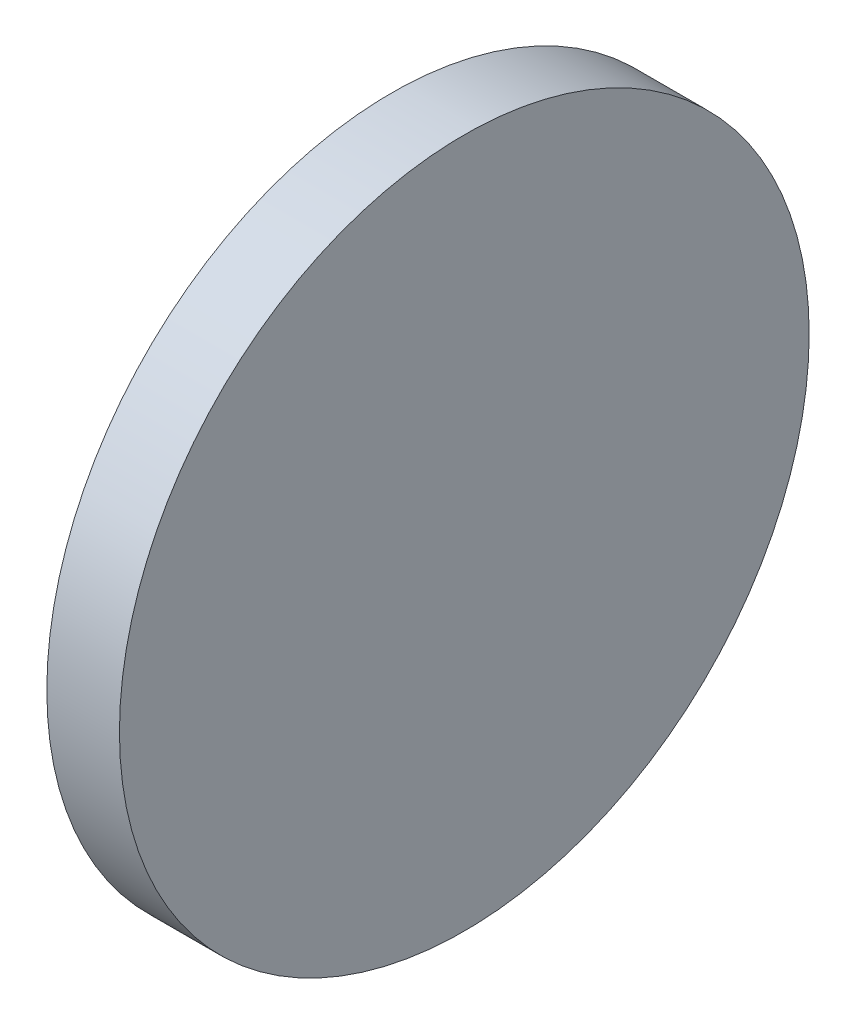
SolidWorks part; units mm, degrees
ref_plane "前视基准面" through (0, 0, 0) normal (0, 0, 1) x (1, 0, 0)
ref_plane "上视基准面" through (0, 0, 0) normal (0, 1, 0) x (1, 0, 0)
ref_plane "右视基准面" through (0, 0, 0) normal (1, 0, 0) x (0, 0, -1)
sketch "草图1" plane through (0, 0, 0) normal (0, 0, 1) x (1, 0, 0)
  line L0 (254.0008, 77.2932) -> (271.5417, 77.2932) construction
  line L1 (260.1617, 77.2932) -> (260.1617, 96.2932)
  line L2 (260.1617, 96.2932) -> (264.1617, 96.2932)
  line L3 (264.1617, 96.2932) -> (264.1617, 77.2932)
  line L4 (264.1617, 77.2932) -> (260.1617, 77.2932)
revolve "旋转1" add sketch "草图1" angle 360 about L0
